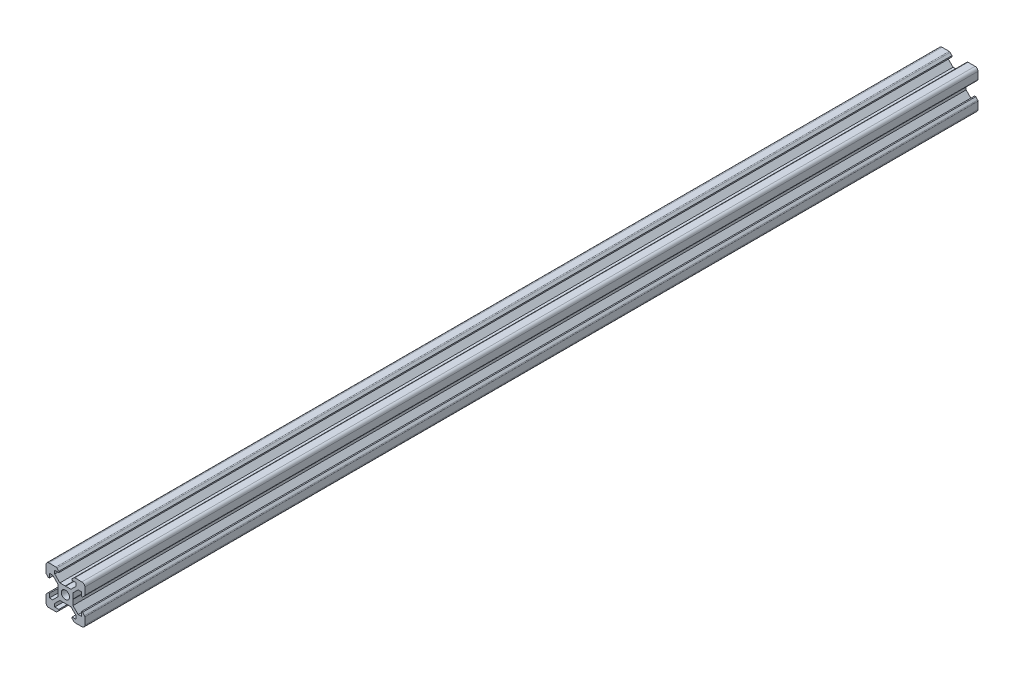
SolidWorks part; units mm, degrees
ref_plane "Front" through (0, 0, 0) normal (0, 0, 1) x (1, 0, 0)
ref_plane "Top" through (0, 0, 0) normal (0, 1, 0) x (1, 0, 0)
ref_plane "Right" through (0, 0, 0) normal (1, 0, 0) x (0, 0, -1)
sketch "Sketch1" plane through (0, 0, 0) normal (0, 0, 1) x (1, 0, 0)
  line L0 (-8.5, 10) -> (-10, 8.5) construction
  line L1 (-8.5, 10) -> (-4.8628, 10)
  line L2 (-10, 8.5) -> (-10, 4.8628)
  line L3 (-8.5, -10) -> (-4.8628, -10)
  line L4 (10, 8.5) -> (10, 4.8628)
  line L5 (-10, 10) -> (10, -10) construction
  line L6 (-10, -10) -> (10, 10) construction
  line L7 (-5.5, -8.2) -> (-3.3865, -8.2)
  line L8 (-8.2, -5.5) -> (-8.2, -3.3865)
  line L9 (-5.5, 8.2) -> (-3.3865, 8.2)
  line L10 (8.2, -5.5) -> (8.2, -3.3865)
  line L11 (-3.9005, 2.8395) -> (-6.561, 5.5)
  line L12 (-6.561, 5.5) -> (-8.2, 5.5)
  line L13 (-2.8395, -3.9005) -> (-0.1, -3.9005)
  line L14 (-3.9005, -2.8395) -> (-3.9005, -0.1)
  line L15 (-2.8395, 3.9005) -> (-0.1, 3.9005)
  line L16 (3.9005, -2.8395) -> (3.9005, -0.1)
  line L17 (-8.2, 3.3865) -> (-8.81, 3.3865)
  line L18 (-8.81, 3.3865) -> (-9.7976, 4.3741)
  line L19 (8.5, 10) -> (10, 8.5) construction
  line L20 (-2.8395, 3.9005) -> (-5.5, 6.561)
  line L21 (-5.5, 6.561) -> (-5.5, 8.2)
  line L22 (-3.3865, 8.2) -> (-3.3865, 8.81)
  line L23 (-3.3865, 8.81) -> (-4.3741, 9.7976)
  line L24 (0, 24.069) -> (0, -33.8154) construction
  line L25 (3.3865, 8.81) -> (4.3741, 9.7976)
  line L26 (3.3865, 8.2) -> (3.3865, 8.81)
  line L27 (5.5, 6.561) -> (5.5, 8.2)
  line L28 (2.8395, 3.9005) -> (5.5, 6.561)
  line L29 (3.3865, 8.2) -> (5.5, 8.2)
  line L30 (4.8628, 10) -> (8.5, 10)
  line L31 (-0.1, 3.9005) -> (0, 3.8005)
  line L32 (0.1, 3.9005) -> (0, 3.8005)
  line L33 (0.1, 3.9005) -> (2.8395, 3.9005)
  line L34 (25.9287, 0) -> (-28.3459, 0) construction
  line L35 (-0.1, -3.9005) -> (0, -3.8005)
  line L36 (0.1, -3.9005) -> (0, -3.8005)
  line L37 (0.1, -3.9005) -> (2.8395, -3.9005)
  line L38 (-3.9005, 0.1) -> (-3.8005, 0)
  line L39 (-3.8005, 0) -> (-3.9005, -0.1)
  line L40 (-3.9005, 0.1) -> (-3.9005, 2.8395)
  line L41 (3.9005, 0.1) -> (3.8005, 0)
  line L42 (3.8005, 0) -> (3.9005, -0.1)
  line L43 (3.9005, 0.1) -> (3.9005, 2.8395)
  line L44 (8.81, 3.3865) -> (9.7976, 4.3741)
  line L45 (8.2, 3.3865) -> (8.81, 3.3865)
  line L46 (6.561, 5.5) -> (8.2, 5.5)
  line L47 (3.9005, 2.8395) -> (6.561, 5.5)
  line L48 (2.8395, -3.9005) -> (5.5, -6.561)
  line L49 (3.9005, -2.8395) -> (6.561, -5.5)
  line L50 (-2.8395, -3.9005) -> (-5.5, -6.561)
  line L51 (-3.9005, -2.8395) -> (-6.561, -5.5)
  line L52 (6.561, -5.5) -> (8.2, -5.5)
  line L53 (-6.561, -5.5) -> (-8.2, -5.5)
  line L54 (-8.81, -3.3865) -> (-9.7976, -4.3741)
  line L55 (-8.2, -3.3865) -> (-8.81, -3.3865)
  line L56 (8.81, -3.3865) -> (9.7976, -4.3741)
  line L57 (8.2, -3.3865) -> (8.81, -3.3865)
  line L58 (8.2, 3.3865) -> (8.2, 5.5)
  line L59 (10, -4.8628) -> (10, -8.5)
  line L60 (-8.2, 3.3865) -> (-8.2, 5.5)
  line L61 (-10, -4.8628) -> (-10, -8.5)
  line L62 (-3.3865, -8.81) -> (-4.3741, -9.7976)
  line L63 (-3.3865, -8.2) -> (-3.3865, -8.81)
  line L64 (3.3865, -8.81) -> (4.3741, -9.7976)
  line L65 (3.3865, -8.2) -> (3.3865, -8.81)
  line L66 (-5.5, -6.561) -> (-5.5, -8.2)
  line L67 (5.5, -6.561) -> (5.5, -8.2)
  line L68 (3.3865, -8.2) -> (5.5, -8.2)
  line L69 (4.8628, -10) -> (8.5, -10)
  circle A0 centre (0, 0) radius 2.1
  arc A1 (-8.5, 10) -> (-10, 8.5) centre (-8.5, 8.5) ccw
  arc A2 (10, 8.5) -> (8.5, 10) centre (8.5, 8.5) ccw
  arc A3 (-4.3741, 9.7976) -> (-4.8628, 10) centre (-4.8628, 9.3088) ccw
  arc A4 (4.8628, 10) -> (4.3741, 9.7976) centre (4.8628, 9.3088) ccw
  arc A5 (-8.5, -10) -> (-10, -8.5) centre (-8.5, -8.5) cw
  arc A6 (9.7976, 4.3741) -> (10, 4.8628) centre (9.3088, 4.8628) ccw
  arc A7 (-10, 4.8628) -> (-9.7976, 4.3741) centre (-9.3088, 4.8628) ccw
  arc A8 (-10, -4.8628) -> (-9.7976, -4.3741) centre (-9.3088, -4.8628) cw
  arc A9 (9.7976, -4.3741) -> (10, -4.8628) centre (9.3088, -4.8628) cw
  arc A10 (10, -8.5) -> (8.5, -10) centre (8.5, -8.5) cw
  arc A11 (-4.3741, -9.7976) -> (-4.8628, -10) centre (-4.8628, -9.3088) cw
  arc A12 (4.8628, -10) -> (4.3741, -9.7976) centre (4.8628, -9.3088) cw
  point P17 (-9.25, 9.25)
  point P21 (9.25, 9.25)
  dimension "D2" = 4.2
  dimension "D4" = 1.5
  dimension "D3" = 20
  dimension "D5" = 0.529
  dimension "D6" = 6.773
  dimension "D7" = 90
  dimension "D8" = 11
  dimension "D9" = 0.61
  dimension "D10" = 0.1
  dimension "D11" = 0.1
  dimension "D12" = 0.1
  dimension "D13" = 0.1
  dimension "D14" = 5.679
  dimension "D15" = 1.639
  dimension "D16" = 1.8
  dimension "D17" = 90
  dimension "D18" = 6.773
  dimension "D19" = 90
extrude "Boss-Extrude1" add sketch "Sketch1" along normal blind 460
